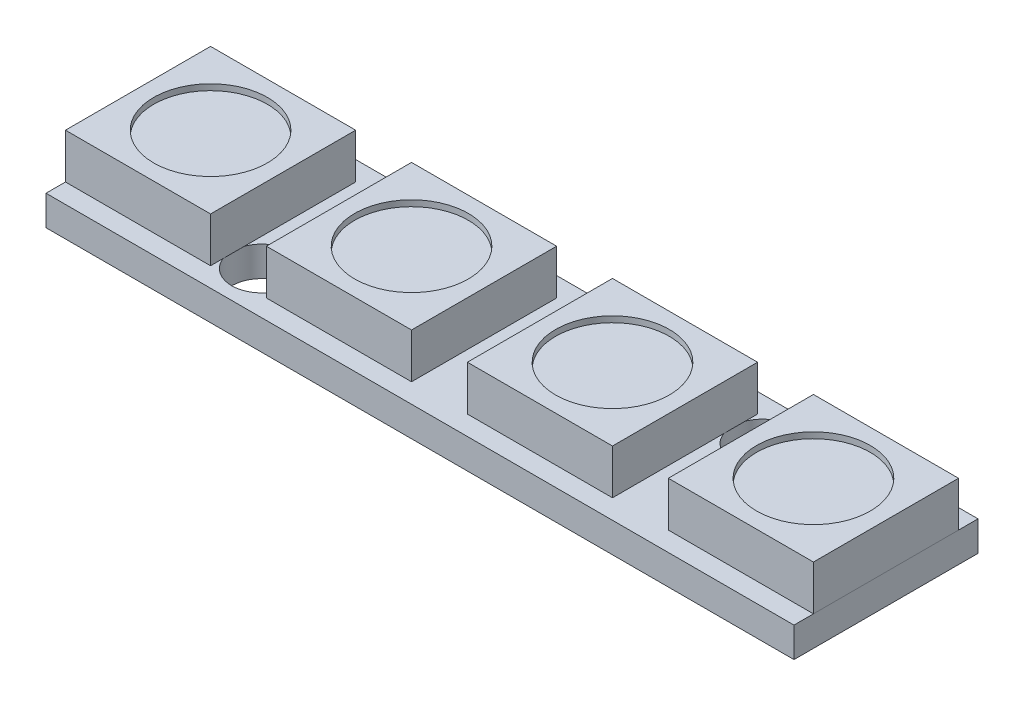
SolidWorks part; units mm, degrees
ref_plane "Front Plane" through (0, 0, 0) normal (0, 0, 1) x (1, 0, 0)
ref_plane "Top Plane" through (0, 0, 0) normal (0, 1, 0) x (1, 0, 0)
ref_plane "Right Plane" through (0, 0, 0) normal (1, 0, 0) x (0, 0, -1)
sketch "Sketch1" plane through (0, 0, 0) normal (0, 1, 0) x (1, 0, 0)
  line L1 (-12.5, 3.075) -> (12.5, 3.075)
  line L2 (-12.5, 3.075) -> (-12.5, -3.075)
  line L3 (-12.5, -3.075) -> (12.5, -3.075)
  line L4 (12.5, 3.075) -> (12.5, -3.075)
  line L5 (-12.5, 3.075) -> (12.5, -3.075) construction
  line L6 (-12.5, -3.075) -> (12.5, 3.075) construction
  point P0 (0, 0)
  dimension "D1" = 25
  dimension "D2" = 6.15
extrude "Boss-Extrude1" add sketch "Sketch1" along normal blind 1
sketch "Sketch2" plane through (0, 1, 0) normal (0, 1, 0) x (1, 0, 0)
  line L0 (-12.5, 0) -> (12.5, 0) construction
  line L1 (-12.5, 3.075) -> (-12.5, -3.075) construction
  line L2 (12.5, -3.075) -> (12.5, 3.075) construction
  line L3 (0, 3.075) -> (0, -3.075) construction
  line L4 (12.5, 3.075) -> (-12.5, 3.075) construction
  line L5 (-12.5, -3.075) -> (12.5, -3.075) construction
  line L6 (-0.9333, 2.425) -> (-0.9333, -2.425)
  line L7 (-12.5, 2.425) -> (-7.65, 2.425)
  line L8 (-12.5, 2.425) -> (-12.5, -2.425)
  line L9 (-12.5, -2.425) -> (-7.65, -2.425)
  line L10 (-7.65, 2.425) -> (-7.65, -2.425)
  line L11 (-12.5, 2.425) -> (-7.65, -2.425) construction
  line L12 (-12.5, -2.425) -> (-7.65, 2.425) construction
  line L13 (-5.7833, -2.425) -> (-0.9333, -2.425)
  line L14 (-5.7833, 2.425) -> (-5.7833, -2.425)
  line L15 (-5.7833, 2.425) -> (-0.9333, 2.425)
  line L16 (5.7833, 2.425) -> (5.7833, -2.425)
  line L17 (0.9333, -2.425) -> (5.7833, -2.425)
  line L18 (0.9333, 2.425) -> (0.9333, -2.425)
  line L19 (0.9333, 2.425) -> (5.7833, 2.425)
  line L20 (12.5, 2.425) -> (12.5, -2.425)
  line L21 (7.65, -2.425) -> (12.5, -2.425)
  line L22 (7.65, 2.425) -> (7.65, -2.425)
  line L23 (7.65, 2.425) -> (12.5, 2.425)
  point P12 (-10.075, 0)
  dimension "D1" = 4.85
  dimension "D2" = 4
extrude "Boss-Extrude2" add sketch "Sketch2" along normal blind 1.5 separate body
sketch "Sketch3" plane through (0, 1, 0) normal (0, 1, 0) x (1, 0, 0)
  line L0 (-7.65, 0) -> (-5.7833, 0) construction
  line L1 (-7.65, -2.425) -> (-7.65, 2.425) construction
  line L3 (-6.7167, 0) -> (-6.7167, -3.075) construction
  line L4 (-12.5, -3.075) -> (12.5, -3.075) construction
  line L5 (0, 1.5648) -> (0, -1.0518) construction
  line L7 (-2.2575, 0) -> (3.2836, 0) construction
  line L8 (-5.7833, 2.425) -> (-5.7833, -2.425) construction
  circle A0 centre (-6.7167, -1.65) radius 1
  circle A1 centre (6.7167, -1.65) radius 1
  circle A2 centre (6.7167, 1.65) radius 1
  point P4 (0, 0)
  dimension "D1" = 2
  dimension "D2" = 3.3
extrude "Cut-Extrude1" cut sketch "Sketch3" against normal up to next (1 mm away) contours A0 | A2
sketch "Sketch4" plane through (0, 2.5, 0) normal (0, 1, 0) x (1, 0, 0)
  line L0 (-12.5, 2.425) -> (-7.65, -2.425) construction
  line L1 (-5.7833, 2.425) -> (-0.9333, -2.425) construction
  line L2 (0.9333, 2.425) -> (5.7833, -2.425) construction
  line L3 (7.65, 2.425) -> (12.5, -2.425) construction
  line L4 (-0.9333, 2.425) -> (-5.7833, 2.425) construction
  line L5 (-5.7833, 2.425) -> (-5.7833, -2.425) construction
  line L6 (12.5, -2.425) -> (12.5, 2.425) construction
  circle A0 centre (-10.075, 0) radius 1.9
  circle A1 centre (-3.3583, 0) radius 1.9
  circle A2 centre (3.3583, 0) radius 1.9
  circle A3 centre (10.075, 0) radius 1.9
  point P24 (-12.5, 2.425)
  point P26 (-7.65, -2.425)
  point P28 (-5.7833, 2.425)
  point P31 (-0.9333, -2.425)
  point P33 (-5.7833, 2.425)
  point P36 (0.9333, 2.425)
  point P38 (5.7833, -2.425)
  point P40 (12.5, -2.425)
  point P43 (7.65, 2.425)
  point P44 (12.5, -2.425)
  dimension "D1" = 3.8
extrude "Cut-Extrude2" cut sketch "Sketch4" against normal blind 0.2
sketch "Sketch5" plane through (0, 0, 0) normal (0, -1, 0) x (1, 0, 0)
  line L0 (-12.5, 1.475) -> (12.5, 1.475) construction
  line L1 (-12.5, -3.075) -> (-12.5, 3.075) construction
  line L2 (12.5, 3.075) -> (12.5, -3.075) construction
  line L3 (0, 3.075) -> (0, -3.075) construction
  line L4 (-12.5, 3.075) -> (12.5, 3.075) construction
  line L5 (12.5, -3.075) -> (-12.5, -3.075) construction
  circle A0 centre (0, 1.475) radius 0.8
  circle A1 centre (2.54, 1.475) radius 0.8
  circle A2 centre (-2.54, 1.475) radius 0.8
  dimension "D2" = 1.6
  dimension "D1" = 1.6
  dimension "D4" = 2.54
  dimension "D3" = 2
extrude "Cut-Extrude3" cut sketch "Sketch5" against normal blind 0.01
